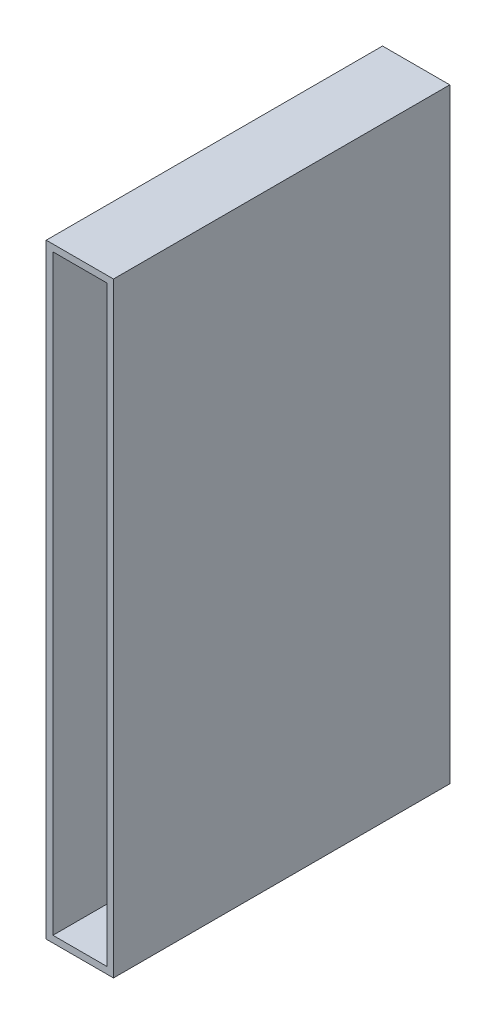
SolidWorks part; units mm, degrees
material "Caoutchouc"
ref_plane "Plan de face" through (0, 0, 0) normal (0, 0, 1) x (1, 0, 0)
ref_plane "Plan de dessus" through (0, 0, 0) normal (0, 1, 0) x (1, 0, 0)
ref_plane "Plan de droite" through (0, 0, 0) normal (1, 0, 0) x (0, 0, -1)
sketch "Esquisse1" plane through (0, 0, 0) normal (0, 0, 1) x (1, 0, 0)
  line L0 (0, 180) -> (0, 0)
  line L1 (0, 180) -> (20, 180)
  line L2 (20, 180) -> (20, 0)
  line L3 (20, 0) -> (0, 0)
  line L4 (2, 178) -> (2, 2)
  line L5 (2, 2) -> (18, 2)
  line L6 (18, 2) -> (18, 178)
  line L7 (18, 178) -> (2, 178)
  dimension "D1" = 2
  dimension "D2" = 2
  dimension "D3" = 2
  dimension "D4" = 2
  dimension "D5" = 180
  dimension "D6" = 16
extrude "Boss.-Extru.2" add sketch "Esquisse1" along normal blind 100 contours L4 L5 L6 L7 | L0 L3 L2 L1
